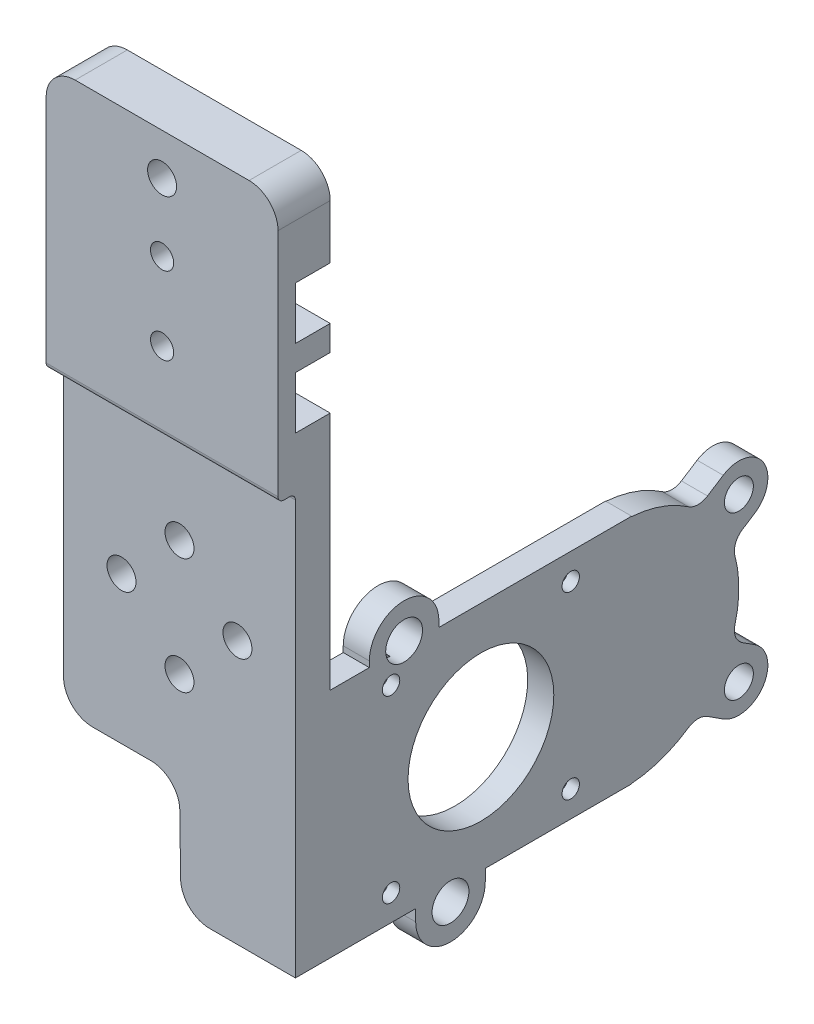
SolidWorks part; units mm, degrees
ref_plane "Front Plane" through (0, 0, 0) normal (0, 0, 1) x (1, 0, 0)
ref_plane "Top Plane" through (0, 0, 0) normal (0, 1, 0) x (1, 0, 0)
ref_plane "Right Plane" through (0, 0, 0) normal (1, 0, 0) x (0, 0, -1)
sketch "Sketch2" plane through (0, 0, 0) normal (0, 0, 1) x (1, 0, 0)
  line L0 (0, 35.4) -> (0, 15.4) construction
  line L5 (-20, 45.4) -> (20, 45.4)
  line L6 (-20, 45.4) -> (-20, -20)
  line L7 (-20, -20) -> (20, -20)
  line L8 (20, 45.4) -> (20, -20)
  line L9 (-10, 25.4) -> (10, 25.4) construction
  circle A1 centre (0, 35.4) radius 2.5
  circle A2 centre (0, 15.4) radius 2.5
  circle A3 centre (-10, 25.4) radius 2.5
  circle A4 centre (10, 25.4) radius 2.5
  dimension "D3" = 5
  dimension "D1" = 10
  dimension "D2" = 20
  dimension "D4" = 40
  dimension "D5" = 65.4
  dimension "D6" = 10
  dimension "D7" = 14.1421
  dimension "D8" = 35.4
extrude "Boss-Extrude1" add sketch "Sketch2" against normal blind 6
sketch "Sketch3" plane through (0, 0, -6) normal (0, 0, -1) x (-1, 0, 0)
  line L0 (20, -20) -> (-20, -20) construction
  line L1 (-20, 20) -> (-15.5, 20)
  line L2 (-20, 20) -> (-20, -20)
  line L3 (-20, -20) -> (-15.5, -20)
  line L4 (-15.5, 20) -> (-15.5, -20)
  dimension "D1" = 4.5
  dimension "D2" = 40
extrude "Boss-Extrude2" add sketch "Sketch3" along normal blind 52
sketch "Sketch4" plane through (15.5, 0, 0) normal (-1, 0, 0) x (0, 0, 1)
  line L0 (-58, -20) -> (-58, 20) construction
  line L1 (-58, 20) -> (-6, 20) construction
  circle A0 centre (-32, 0) radius 12.5732
  circle A1 centre (-16.5, 15.5) radius 1.5
  circle A2 centre (-16.5, -15.5) radius 1.5
  circle A3 centre (-47.5, -15.5) radius 1.5
  circle A4 centre (-47.5, 15.5) radius 1.5
  point P0 (0, 0)
  point P3 (-58, 0)
  point P10 (-32, 20)
  point P19 (-32, 0)
  dimension "D3" = 15.5
  dimension "D1" = 15.5
  dimension "D2" = 4
extrude "Cut-Extrude1" cut sketch "Sketch4" against normal up to next
sketch "Sketch5" plane through (0, 0, -6) normal (0, 0, -1) x (-1, 0, 0)
  circle A0 centre (0, 35.4) radius 4.5
  circle A2 centre (10, 25.4) radius 4.5
  circle A3 centre (0, 15.4) radius 4.5
  circle A4 centre (-10, 25.4) radius 4.5
  point P3 (0, 10)
  dimension "D1" = 9
  dimension "D2" = 20
  dimension "D3" = 20
  dimension "D4" = 14.1421
  dimension "D5" = 35.4
extrude "Cut-Extrude2" cut sketch "Sketch5" against normal blind 1.5
sketch "Sketch6" plane through (15.5, 0, 0) normal (-1, 0, 0) x (0, 0, 1)
  circle A0 centre (-16.5, 15.5) radius 3
  circle A1 centre (-47.5, 15.5) radius 3
  circle A2 centre (-47.5, -15.5) radius 3
  circle A3 centre (-16.5, -15.5) radius 3
  dimension "D1" = 6
extrude "Cut-Extrude3" cut sketch "Sketch6" against normal blind 2.5
fillet "Fillet1" radius 5 1 edges at (-20, -20, -3)
sketch "Sketch7" plane through (0, 45.4, 0) normal (0, 1, 0) x (1, 0, 0)
  line L0 (11.3015, -6) -> (-12.8253, -6)
  line L5 (-12.8253, -6) -> (-12.8253, -4.5)
  line L16 (6.4761, 3.0522) -> (-7.9999, 3.0522)
  line L22 (20, 6) -> (-20, 6) construction
  line L23 (6.4761, -4.5) -> (6.4761, -3.0522)
  line L26 (11.3015, 6) -> (11.3015, 4.5)
  line L27 (-12.8253, 3.0522) -> (-12.8253, -3.0522)
  line L28 (11.3015, 3.0522) -> (11.3015, -3.0522)
  line L29 (-7.9999, 4.5) -> (-12.8253, 4.5)
  line L30 (-9.7777, 3.0522) -> (-12.8253, 3.0522)
  line L31 (-7.9999, 4.5) -> (-7.9999, 3.0522)
  line L32 (-9.7777, 3.0522) -> (-9.7777, 1.6022)
  line L33 (8.2539, 1.6022) -> (-9.7777, 1.6022)
  line L34 (8.2539, 3.0522) -> (8.2539, 1.6022)
  line L35 (11.3015, 3.0522) -> (8.2539, 3.0522)
  line L36 (11.3015, 4.5) -> (6.4761, 4.5)
  line L37 (6.4761, 4.5) -> (6.4761, 3.0522)
  line L38 (-12.8253, 6) -> (-12.8253, 4.5)
  line L40 (11.3015, 6) -> (-12.8253, 6)
  line L41 (11.3015, -4.5) -> (6.4761, -4.5)
  line L42 (11.3015, -3.0522) -> (8.2539, -3.0522)
  line L43 (8.2539, -3.0522) -> (8.2539, -1.6022)
  line L44 (8.2539, -1.6022) -> (-9.7777, -1.6022)
  line L45 (-9.7777, -3.0522) -> (-9.7777, -1.6022)
  line L46 (-7.9999, -4.5) -> (-7.9999, -3.0522)
  line L47 (-9.7777, -3.0522) -> (-12.8253, -3.0522)
  line L48 (-7.9999, -4.5) -> (-12.8253, -4.5)
  line L49 (11.3015, -6) -> (11.3015, -4.5)
  line L52 (6.4761, -3.0522) -> (-7.9999, -3.0522)
sketch "Sketch9" plane through (15.5, 0, 0) normal (-1, 0, 0) x (0, 0, 1)
  line L0 (-32.75, -22) -> (-32.75, -18.4344)
  line L3 (-32.75, -18.4344) -> (-20.75, -18.4344)
  line L5 (-20.75, -18.4344) -> (-20.75, -22)
  line L6 (-24.75, 21) -> (-24.75, 17.6037)
  line L9 (-24.75, 17.6037) -> (-12.75, 17.6037)
  line L11 (-12.75, 17.6037) -> (-12.75, 21)
  circle A0 centre (-18.75, 21) radius 3.175
  arc A1 (-12.75, 21) -> (-24.75, 21) centre (-18.75, 21) ccw
  circle A2 centre (-26.75, -22) radius 3.175
  arc A3 (-32.75, -22) -> (-20.75, -22) centre (-26.75, -22) ccw
  arc A5 (-32.7128, -22.6667) -> (-20.7872, -22.6667) centre (-26.75, -22) ccw construction
  dimension "D1" = 6.35
  dimension "D2" = 6.35
sketch "Sketch11" plane through (15.5, 0, 0) normal (-1, 0, 0) x (0, 0, 1)
  line L0 (-56.5, 20) -> (-56.5, -20)
  line L1 (-73.7993, 18.2079) -> (-69.332, 15.3408)
  line L2 (-79.2007, 9.7921) -> (-75.1596, 7.1985)
  line L3 (-79.2007, -9.7921) -> (-75.1596, -7.1985)
  line L4 (-73.7993, -18.2079) -> (-69.332, -15.3408)
  line L7 (-58, -20) -> (0, -20) construction
  arc A0 (-56.5, 20) -> (-56.5, -20) centre (-56.5, 0) ccw
  arc A1 (-75.8257, 5.1494) -> (-75.8257, -5.1494) centre (-56.5, 0) ccw construction
  circle A2 centre (-76.5, 14) radius 2.5
  arc A3 (-73.7993, 18.2079) -> (-79.2007, 9.7921) centre (-76.5, 14) ccw
  circle A4 centre (-76.5, -14) radius 2.5
  arc A5 (-79.2007, -9.7921) -> (-73.7993, -18.2079) centre (-76.5, -14) ccw
  line M15 (-58, 20) -> (-58, -20)
extrude "Boss-Extrude6" add sketch "Sketch11" against normal up to surface (4.5 mm away) contours A0 M15 | L1 A3 L2 A0 A2 | L3 A5 L4 A0 A4 up to face at (20, 17, -47.5)
fillet "Fillet2" radius 3 4 edges at (17.75, -15.3408, -69.332) (17.75, 15.3408, -69.332) (17.75, -7.1985, -75.1596) (17.75, 7.1985, -75.1596)
sketch "Sketch15" plane through (15.5, 0, 0) normal (-1, 0, 0) x (0, 0, 1)
  circle A0 centre (-16.5, 15.5) radius 3
  circle A1 centre (-16.5, 15.5) radius 3 construction
extrude "Boss-Extrude15" add sketch "Sketch9" against normal up to surface (4.5 mm away) up to face at (20, 17, -47.5)
sketch "Sketch24" plane through (15.5, 0, 0) normal (-1, 0, 0) x (0, 0, 1)
  circle A0 centre (-18.75, 21) radius 3.175
  circle A1 centre (-26.75, -22) radius 3.175
  arc A2 (-29.2159, -20) -> (-24.2841, -20) centre (-26.75, -22) ccw construction
  dimension "D1" = 6.35
extrude "Cut-Extrude11" cut sketch "Sketch24" against normal up to surface (4.5 mm away) up to face at (20, 3.1714, -47.2875)
extrude "Cut-Extrude12" cut sketch "Sketch15" against normal up to surface (2.5 mm away) up to face at (18, 15.0519, -16.5)
sketch "Sketch25" plane through (0, 45.4, 0) normal (0, 1, 0) x (1, 0, 0)
  line L0 (20, 6) -> (20, 0) construction
  line L1 (20, -3) -> (-20, -3)
  line L2 (20, -3) -> (20, 6)
  line L3 (20, 6) -> (-20, 6)
  line L4 (-20, -3) -> (-20, 6)
  line L7 (4.5, 6) -> (-4.5, 6) construction
  line L8 (-20, 6) -> (-20, 0) construction
  dimension "D2" = 9
extrude "Boss-Extrude16" add sketch "Sketch25" along normal blind 52.75
sketch "Sketch28" plane through (0, 0, 3) normal (0, 0, 1) x (1, 0, 0)
  line L0 (20, 98.15) -> (20, 45.4) construction
  line L1 (-20, 45.4) -> (20, 45.4)
  line L2 (-20, 45.4) -> (-20, 47.4)
  line L3 (-20, 47.4) -> (20, 47.4)
  line L4 (20, 45.4) -> (20, 47.4)
  dimension "D1" = 2
extrude "Cut-Extrude15" cut sketch "Sketch28" against normal up to surface (3 mm away) up to face at (12.5, 25.4, 0)
sketch "Sketch33" plane through (0, 0, 3) normal (0, 0, 1) x (1, 0, 0)
  line L0 (20, 98.15) -> (20, 47.4) construction
  line L1 (-20, 47.4) -> (20, 47.4)
  line L2 (-20, 47.4) -> (-20, 52.4)
  line L3 (-20, 52.4) -> (20, 52.4)
  line L4 (20, 47.4) -> (20, 52.4)
  dimension "D1" = 5
extrude "Cut-Extrude18" cut sketch "Sketch33" against normal up to surface (3 mm away) up to face at (12.5, 25.4, 0)
fillet "Fillet7" radius 1 2 edges at (0, 52.4, 0) (0, 52.4, 3)
sketch "Sketch29" plane through (0, 0, 3) normal (0, 0, 1) x (1, 0, 0)
  line L0 (-20, 98.15) -> (-20, 53.4) construction
  line L1 (-20, 74.4424) -> (20, 74.4424)
  line L2 (-20, 74.4424) -> (-20, 65.4)
  line L3 (-20, 65.4) -> (20, 65.4)
  line L4 (20, 74.4424) -> (20, 65.4)
  line L5 (20, 98.15) -> (20, 53.4) construction
  line L6 (20, 52.4) -> (-20, 52.4) construction
  line L10 (-20, 80.7924) -> (20, 80.7924)
  line L11 (-20, 80.7924) -> (-20, 89.8348)
  line L12 (-20, 89.8348) -> (20, 89.8348)
  line L13 (20, 80.7924) -> (20, 89.8348)
  dimension "D1" = 9.0424
  dimension "D2" = 13
  dimension "D3" = 6.35
fillet "Fillet8" radius 5 2 edges at (-20, 98.15, -1.5) (20, 98.15, -1.5)
sketch "Sketch31" plane through (0, 0, -6) normal (0, 0, -1) x (-1, 0, 0)
  line L0 (20, 93.15) -> (20, -15) construction
  line L1 (-20, 70.4424) -> (20, 70.4424)
  line L2 (-20, 70.4424) -> (-20, 61.4)
  line L3 (-20, 61.4) -> (20, 61.4)
  line L4 (20, 70.4424) -> (20, 61.4)
  line L5 (-20, 93.15) -> (-20, 20) construction
  line L7 (-20, 83.8348) -> (20, 83.8348)
  line L8 (-20, 83.8348) -> (-20, 74.7924)
  line L9 (-20, 74.7924) -> (20, 74.7924)
  line L10 (20, 83.8348) -> (20, 74.7924)
  line L11 (-20, 52.4) -> (20, 52.4) construction
  dimension "D1" = 9.0424
  dimension "D2" = 4.35
  dimension "D3" = 9.0424
  dimension "D4" = 9
extrude "Cut-Extrude16" cut sketch "Sketch31" against normal blind 6
sketch "Sketch32" plane through (0, 0, 0) normal (0, 0, -1) x (-1, 0, 0)
  line L0 (-20, 83.8348) -> (-20, 74.7924) construction
  line L1 (20, 83.8348) -> (-20, 83.8348) construction
  line L2 (-20, 70.4424) -> (-20, 61.4) construction
  line L3 (20, 70.4424) -> (-20, 70.4424) construction
  circle A0 centre (0, 79.3136) radius 2
  circle A1 centre (0, 65.9212) radius 2
  point P6 (-20, 79.3136)
  point P9 (0, 83.8348)
  point P13 (-20, 65.9212)
  point P16 (0, 70.4424)
  dimension "D1" = 4
  dimension "D2" = 4
extrude "Cut-Extrude17" cut sketch "Sketch32" against normal through all
sketch "Sketch34" plane through (0, 0, -6) normal (0, 0, -1) x (-1, 0, 0)
  line L0 (20, 83.8348) -> (-20, 83.8348) construction
  line L1 (-20, 83.8348) -> (-20, 98.15) construction
  line L2 (-15, 98.15) -> (15, 98.15) construction
  circle A0 centre (0, 90.9924) radius 2.5
  point P2 (0, 0)
  point P6 (0, 83.8348)
  point P11 (0, 0)
  point P12 (-20, 90.9924)
  dimension "D1" = 5
extrude "Cut-Extrude19" cut sketch "Sketch34" against normal up to surface (9 mm away) up to face at (-2, 79.3136, 3)
sketch "Sketch35" plane through (0, 0, -6) normal (0, 0, -1) x (-1, 0, 0)
  line L0 (-0.25, -20) -> (0, 0)
  line L1 (15, -20) -> (-15.5, -20) construction
  line L2 (0, 0) -> (20, 0)
  line L3 (20, 61.4) -> (20, -15) construction
  line L4 (20, 0) -> (20, -20)
  line L5 (20, -20) -> (-0.25, -20)
extrude "Cut-Extrude20" cut sketch "Sketch35" against normal blind 10
fillet "Fillet9" radius 5 3 edges at (0.25, -20, -3) (0, 0, -3) (-20, 0, -3)
